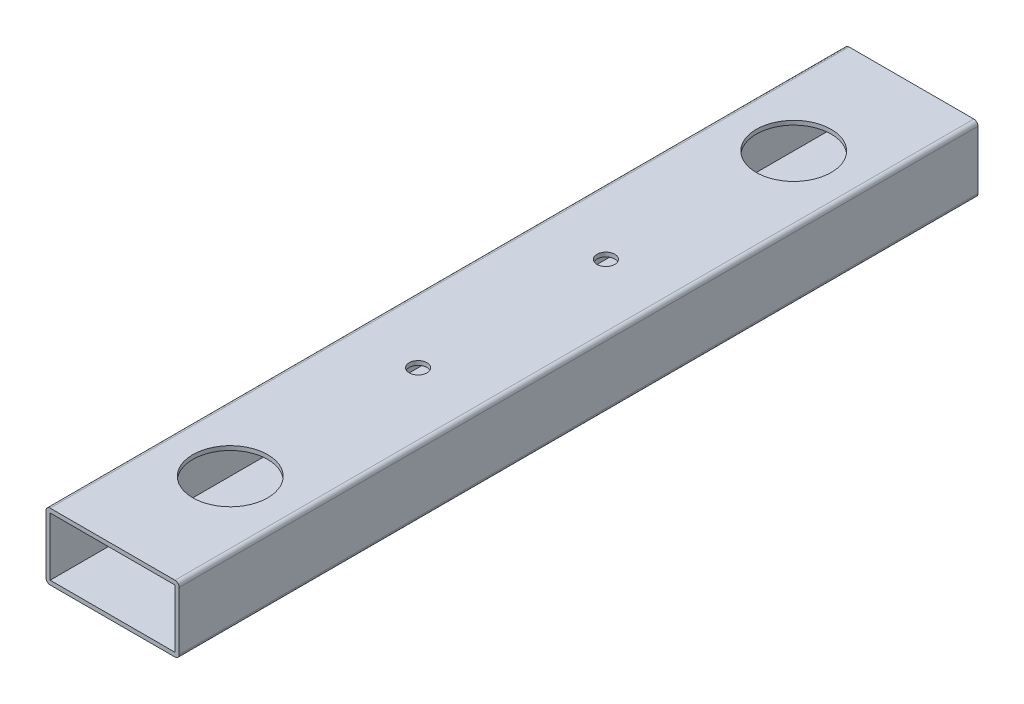
SolidWorks part; units mm, degrees
ref_plane "Front Plane" through (0, 0, 0) normal (0, 0, 1) x (1, 0, 0)
ref_plane "Top Plane" through (0, 0, 0) normal (0, 1, 0) x (1, 0, 0)
ref_plane "Right Plane" through (0, 0, 0) normal (1, 0, 0) x (0, 0, -1)
sketch "Sketch1" plane through (0, 0, 0) normal (0, 0, 1) x (1, 0, 0)
  line L0 (-23.8125, 11.1125) -> (23.8125, 11.1125)
  line L1 (-23.8125, -12.7) -> (23.8125, -12.7)
  line L2 (-25.4, -11.1125) -> (-25.4, 11.1125)
  line L3 (-23.8125, 12.7) -> (23.8125, 12.7)
  line L4 (25.4, -11.1125) -> (25.4, 11.1125)
  line L5 (-25.4, -12.7) -> (25.4, 12.7) construction
  line L6 (-25.4, 12.7) -> (25.4, -12.7) construction
  line L7 (23.8125, -11.1125) -> (23.8125, 11.1125)
  line L8 (-23.8125, -11.1125) -> (23.8125, -11.1125)
  line L9 (-23.8125, -11.1125) -> (-23.8125, 11.1125)
  line L10 (-25.4, -12.7) -> (25.4, -12.7) construction
  line L11 (-25.4, -12.7) -> (-25.4, 12.7) construction
  line L12 (25.4, -12.7) -> (25.4, 12.7) construction
  line L13 (-25.4, 12.7) -> (25.4, 12.7) construction
  arc A0 (-23.8125, -12.7) -> (-25.4, -11.1125) centre (-23.8125, -11.1125) cw
  arc A1 (23.8125, -12.7) -> (25.4, -11.1125) centre (23.8125, -11.1125) ccw
  arc A2 (23.8125, 12.7) -> (25.4, 11.1125) centre (23.8125, 11.1125) cw
  arc A3 (-25.4, 11.1125) -> (-23.8125, 12.7) centre (-23.8125, 11.1125) cw
  point P0 (0, 0)
  dimension "D4" = 1.5875
  dimension "D1" = 25.4
  dimension "D2" = 50.8
  dimension "D3" = 1.5875
extrude "Boss-Extrude1" add sketch "Sketch1" along normal blind 304.8
sketch "Sketch2" plane through (0, 12.7, 0) normal (0, 1, 0) x (1, 0, 0)
  line L0 (23.8125, 0) -> (-23.8125, 0) construction
  line L2 (0, -259.9) -> (0, -44.9) construction
  line L3 (0, -44.9) -> (0, 0) construction
  line L5 (0, -259.9) -> (0, -304.8) construction
  line L6 (23.8125, -304.8) -> (-23.8125, -304.8) construction
  circle A8 centre (0, -259.9) radius 14.2875
  circle A9 centre (0, -44.9) radius 14.2875
  point P7 (0, 0)
  dimension "D1" = 215
  dimension "D2" = 28.575
extrude "Cut-Extrude1" cut sketch "Sketch2" against normal up to next and the other way through all
sketch "Sketch3" plane through (0, -12.7, 0) normal (0, -1, 0) x (1, 0, 0)
  circle A2 centre (0, 44.9) radius 12.7
  circle A3 centre (0, 259.9) radius 12.7
  circle A4 centre (0, 259.9) radius 14.2875 construction
  circle A6 centre (0, 44.9) radius 14.2875 construction
  dimension "D1" = 25.4
extrude "Cut-Extrude2" cut sketch "Sketch3" against normal up to next and the other way through all
sketch "Sketch4" plane through (0, 12.7, 0) normal (0, 1, 0) x (1, 0, 0)
  line L0 (0, -44.9) -> (0, -259.9) construction
  line L1 (0, -44.9) -> (0, -259.9) construction
  circle A0 centre (0, -188.2333) radius 3.3782
  circle A1 centre (0, -116.5667) radius 3.3782
  dimension "D3" = 6.7564
  dimension "D1" = 71.6667
  dimension "D2" = 71.6667
extrude "Cut-Extrude3" cut sketch "Sketch4" against normal up to next and the other way through all
sketch "Sketch5" plane through (0, -12.7, 0) normal (0, -1, 0) x (1, 0, 0)
  line L0 (0, 44.9) -> (0, 259.9) construction
  line L1 (0, 44.9) -> (0, 259.9) construction
  circle A0 centre (0, 116.5667) radius 7.9375
  circle A1 centre (0, 188.2333) radius 7.9375
  circle A2 centre (0, 116.5667) radius 3.3782 construction
  circle A3 centre (0, 188.2333) radius 3.3782 construction
  dimension "D1" = 15.875
extrude "Cut-Extrude4" cut sketch "Sketch5" against normal up to next and the other way through all
